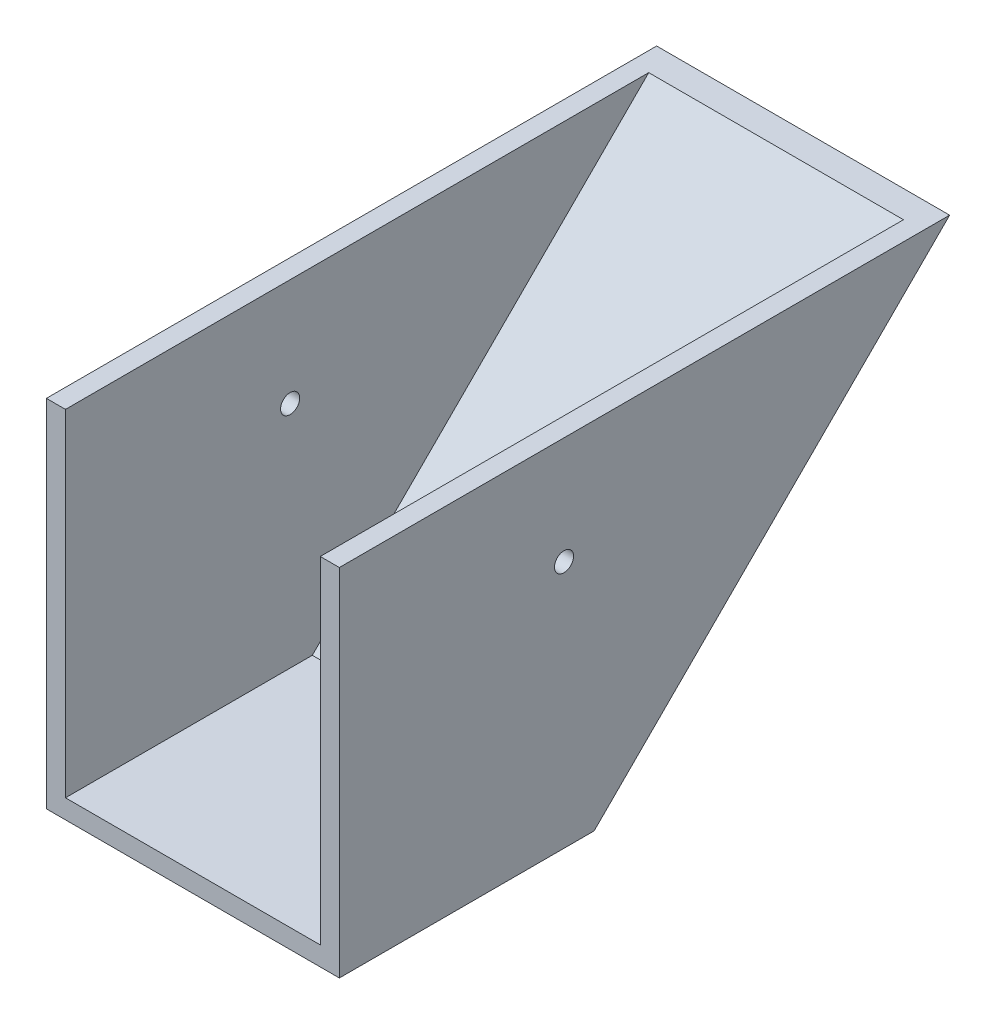
SolidWorks part; units mm, degrees
material "ALUMINUM 6061-T6"
ref_plane "Front Plane" through (0, 0, 0) normal (0, 0, 1) x (1, 0, 0)
ref_plane "Top Plane" through (0, 0, 0) normal (0, 1, 0) x (1, 0, 0)
ref_plane "Right Plane" through (0, 0, 0) normal (1, 0, 0) x (0, 0, -1)
sketch "Sketch2" plane through (0, 0, 0) normal (0, 1, 0) x (1, 0, 0)
  line L1 (-146.05, -317.5) -> (146.05, -317.5)
  line L2 (-146.05, -317.5) -> (-146.05, 317.5)
  line L3 (-146.05, 317.5) -> (146.05, 317.5)
  line L4 (146.05, -317.5) -> (146.05, 317.5)
  line L5 (-146.05, -317.5) -> (146.05, 317.5) construction
  line L6 (-146.05, 317.5) -> (146.05, -317.5) construction
  point P0 (0, 0)
extrude "Boss-Extrude1" add sketch "Sketch2" along normal mid plane 381
sketch "Sketch4" plane through (-146.05, 0, 0) normal (-1, 0, 0) x (0, 0, 1)
  line L0 (-317.5, 190.5) -> (63.5, -190.5)
  line L1 (-317.5, -190.5) -> (317.5, -190.5) construction
  line L2 (-317.5, 190.5) -> (-317.5, -190.5) construction
  line L3 (-317.5, 190.5) -> (-317.5, -190.5)
  line L4 (-317.5, -190.5) -> (63.5, -190.5)
  dimension "D1" = 45
extrude "Cut-Extrude2" cut sketch "Sketch4" against normal blind 381
shell "Shell1" thickness 19.05
sketch "Sketch5" plane through (0, 190.5, 0) normal (0, 1, 0) x (1, 0, 0)
  line L1 (-146.05, 317.5) -> (146.05, 317.5)
  line L2 (-146.05, 317.5) -> (-146.05, -317.5)
  line L3 (-146.05, -317.5) -> (146.05, -317.5)
  line L4 (146.05, 317.5) -> (146.05, -317.5)
extrude "Cut-Extrude3" cut sketch "Sketch5" against normal blind 24.892
sketch "Sketch6" plane through (-146.05, 0, 0) normal (-1, 0, 0) x (0, 0, 1)
  circle A0 centre (93.5173, 56.9612) radius 9.525
extrude "Cut-Extrude4" cut sketch "Sketch6" against normal blind 514.096
sketch "Sketch10" plane through (0, 165.608, 0) normal (0, 1, 0) x (1, 0, 0)
  line L1 (-146.05, 292.608) -> (146.05, 292.608)
  line L2 (-146.05, 292.608) -> (-146.05, -317.5)
  line L3 (-146.05, -317.5) -> (146.05, -317.5)
  line L4 (146.05, 292.608) -> (146.05, -317.5)
extrude "Cut-Extrude7" cut sketch "Sketch10" against normal blind 1.6933
